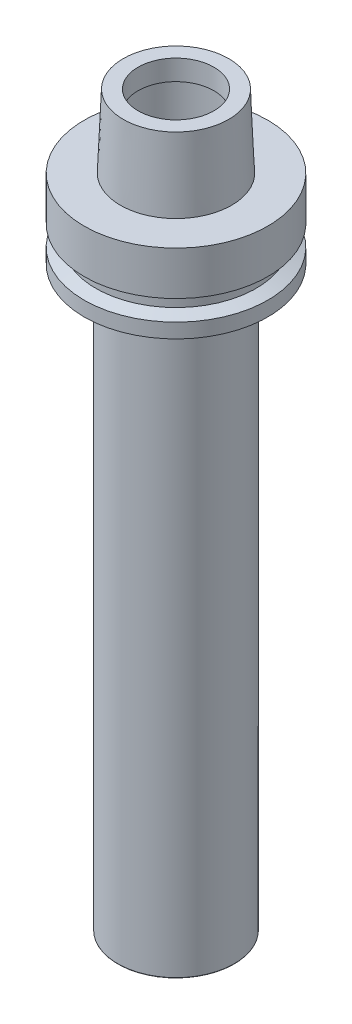
SolidWorks part; units mm, degrees
ref_plane "Front Plane" through (0, 0, 0) normal (0, 0, 1) x (1, 0, 0)
ref_plane "Top Plane" through (0, 0, 0) normal (0, 1, 0) x (1, 0, 0)
ref_plane "Right Plane" through (0, 0, 0) normal (1, 0, 0) x (0, 0, -1)
sketch "Sketch1" plane through (0, 0, 0) normal (0, 0, 1) x (1, 0, 0)
  line L0 (0, 0) -> (0, 66.0974) construction
  line L1 (-13, 252.3) -> (-18.085, 252.3)
  line L2 (-18.085, 252.3) -> (-19.1, 227.3)
  line L3 (-19.1, 227.3) -> (-31.5, 227.3)
  line L4 (-31.5, 227.3) -> (-31.5, 212.3)
  line L5 (-31.5, 212.3) -> (-27.5, 210.8)
  line L6 (-27.5, 210.8) -> (-27.5, 206.8)
  line L7 (-27.5, 206.8) -> (-31.5, 205.3)
  line L8 (-31.5, 205.3) -> (-31.5, 200.3)
  line L9 (-31.5, 200.3) -> (-20, 200.3)
  line L13 (-15.6699, -0.2) -> (-13.5, -0.2)
  line L14 (-13, 252.3) -> (-13, 245.3)
  line L15 (-13, 245.3) -> (-14, 245.3)
  line L16 (-16, 243.3) -> (-16, 225.3)
  line L17 (-14, 223.3) -> (-13, 223.3)
  line L18 (-13, 223.3) -> (-13, 218.3)
  line L19 (-13, 218.3) -> (0, 218.3)
  line L20 (-20, 200.3) -> (-19.75, 200.3)
  line L21 (-20, 200.05) -> (-20, 2.4443)
  line L22 (-19.875, 2.2278) -> (-15.6699, -0.2)
  line L23 (-13.5, -0.2) -> (-13.5, 0)
  line L24 (-13.5, 0) -> (-2.5, 0)
  line L25 (-2.5, 0) -> (-2.5, 15)
  line L26 (-2.5, 15) -> (0, 15)
  line L27 (0, 218.3) -> (0, 15)
  arc A0 (-16, 225.3) -> (-14, 223.3) centre (-14, 225.3) ccw
  arc A1 (-14, 245.3) -> (-16, 243.3) centre (-14, 243.3) ccw
  arc A2 (-19.75, 200.3) -> (-20, 200.05) centre (-19.75, 200.05) ccw
  arc A3 (-19.875, 2.2278) -> (-20, 2.4443) centre (-19.75, 2.4443) cw
  point P33 (-20, 2.3)
  dimension "D6" = 2
  dimension "D22" = 0.25
  dimension "D1" = 25
  dimension "D2" = 36.17
  dimension "D3" = 38.2
  dimension "D4" = 26
  dimension "D5" = 3
  dimension "D7" = 7
  dimension "D8" = 63
  dimension "D9" = 15
  dimension "D10" = 5
  dimension "D11" = 4
  dimension "D14" = 7
  dimension "D15" = 4
  dimension "D17" = 40
  dimension "D20" = 30
  dimension "D21" = 2.5
  dimension "D23" = 200.5
  dimension "D24" = 34
  dimension "D25" = 5
  dimension "D26" = 0.2
  dimension "D27" = 27
  dimension "D28" = 5
  dimension "D29" = 15
revolve "Rivoluzione1" add sketch "Sketch1" angle 360 about L0
move or copy body "Corpo-Sposta/copia1" bodies to move or copy 107 copy no translate (0, -209, 0)
